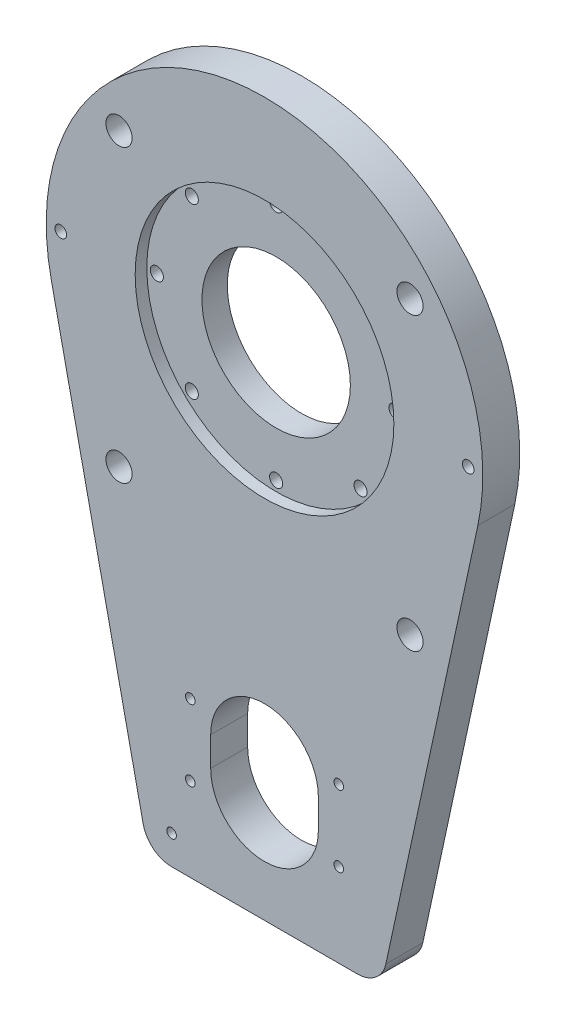
SolidWorks part; units mm, degrees
ref_plane "Front Plane" through (0, 0, 0) normal (0, 0, 1) x (1, 0, 0)
ref_plane "Top Plane" through (0, 0, 0) normal (0, 1, 0) x (1, 0, 0)
ref_plane "Right Plane" through (0, 0, 0) normal (1, 0, 0) x (0, 0, -1)
ref_plane "Plane1" through (0, 0, 12.7) normal (0, 0, 1) x (1, 0, 0)
sketch "Sketch1" plane through (0, 0, 12.7) normal (0, 0, 1) x (1, 0, 0)
  line L0 (40, -170) -> (73.3084, -15.8392)
  line L1 (-73.3084, -15.8392) -> (-40, -170)
  line L2 (-40, -170) -> (40, -170)
  arc A0 (73.3084, -15.8392) -> (-73.3084, -15.8392) centre (0, 0) ccw
extrude "Boss-Extrude1" add sketch "Sketch1" against normal blind 12.7
sketch "Sketch2" plane through (0, 0, 0) normal (0, 0, -1) x (-1, 0, 0)
  line L0 (-18.5, -124) -> (-18.5, -134)
  line L1 (18.5, -134) -> (18.5, -124)
  arc A0 (-18.5, -134) -> (18.5, -134) centre (0, -134) ccw
  arc A1 (18.5, -124) -> (-18.5, -124) centre (0, -124) ccw
extrude "Cut-Extrude1" cut sketch "Sketch2" against normal through all
hole_wizard "Hole1" positions "Sketch4" profile "Sketch3" legacy
sketch "Sketch4" plane through (0, 0, 0) normal (0, 0, -1) x (-1, 0, 0)
  point P0 (-50, -60)
  point P1 (50, -60)
  point P2 (50, 40)
  point P3 (-50, 40)
sketch "Sketch3" plane through (50, -60, 0) normal (1, 0, 0) x (0, 1, 0)
  line L0 (0, 0) -> (0, 12.7)
  line L1 (0, 12.7) -> (4.5, 12.7)
  line L2 (4.5, 12.7) -> (4.5, 0)
  line L3 (4.5, 0) -> (0, 0)
  line L4 (0, 110) -> (0, -10) construction
  dimension "Diameter" = 9
  dimension "Depth" = 12.7
hole_wizard "#4 Clearance Hole1" positions "Sketch6" profile "Sketch5" hole size "#4" standard "ANSI Inch"
sketch "Sketch6" plane through (0, 0, 12.7) normal (0, 0, 1) x (1, 0, 0)
  point P0 (-31.9299, -160)
  point P1 (-25.5, -116.75)
  point P2 (-25.5, -141.25)
  point P3 (25.5, -116.75)
  point P4 (25.5, -141.25)
sketch "Sketch5" plane through (-31.9299, -160, 12.7) normal (1, 0, 0) x (0, -1, 0)
  line L0 (0, 0) -> (0, 12.7)
  line L1 (0, 12.7) -> (1.65, 12.7)
  line L2 (1.65, 12.7) -> (1.65, 0)
  line L5 (1.65, 0) -> (0, 0)
  line L11 (0, -6.35) -> (0, 107.95) construction
  dimension "Thru Hole Dia." = 3.3
  dimension "Thru Hole Depth" = 12.7
hole_wizard "Hole2" positions "Sketch8" profile "Sketch7" legacy
sketch "Sketch8" plane through (0, 0, 12.7) normal (0, 0, 1) x (1, 0, 0)
  point P0 (0, 0)
sketch "Sketch7" plane through (0, 0, 12.7) normal (1, 0, 0) x (0, -1, 0)
  line L0 (0, 0) -> (0, 12.7)
  line L1 (0, 12.7) -> (25.5, 12.7)
  line L2 (25.5, 12.7) -> (25.5, 4)
  line L3 (25.5, 4) -> (44.45, 4)
  line L4 (44.45, 4) -> (44.45, 0)
  line L5 (44.45, 0) -> (0, 0)
  line L6 (0, 110) -> (0, -10) construction
  dimension "Diameter" = 51
  dimension "Depth" = 12.7
  dimension "C-Bore Diameter" = 88.9
  dimension "C-Bore Depth" = 4
hole_wizard "CBORE for #8 Binding Head Machine Screw1" positions "Sketch10" profile "Sketch9" counterbore size "#8" standard "ANSI Inch"
sketch "Sketch10" plane through (0, 0, 0) normal (0, 0, -1) x (-1, 0, 0)
  point P0 (28.9914, 28.9914)
  point P1 (41, 0)
  point P2 (28.9914, -28.9914)
  point P3 (0, -41)
  point P4 (-28.9914, -28.9914)
  point P5 (-41, 0)
  point P6 (-28.9914, 28.9914)
  point P7 (0, 41)
sketch "Sketch9" plane through (-28.9914, 28.9914, 0) normal (1, 0, 0) x (0, 1, 0)
  line L0 (0, 0) -> (0, 12.7)
  line L1 (0, 12.7) -> (2.25, 12.7)
  line L3 (2.25, 12.7) -> (2.25, 4)
  line L4 (2.25, 4) -> (4.125, 4)
  line L5 (4.125, 4) -> (4.125, 0)
  line L7 (4.125, 0) -> (0, 0)
  line L11 (0, -6.35) -> (0, 107.95) construction
  dimension "Thru Hole Dia." = 4.5
  dimension "Thru Hole Depth" = 12.7
  dimension "C'Bore Dia." = 8.25
  dimension "C'Bore Depth" = 4
fillet "Fillet1" radius 10 2 edges at (-40, -170, 6.35) (40, -170, 6.35)
sketch "Sketch11" plane through (0, 0, 12.7) normal (0, 0, 1) x (1, 0, 0)
  line L0 (-75, 0) -> (75, 0) construction
  arc A0 (73.3084, -15.8392) -> (-73.3084, -15.8392) centre (0, 0) ccw construction
  circle A1 centre (-70, 0) radius 2
  circle A2 centre (70, 0) radius 2
  dimension "D1" = 4
  dimension "D2" = 4
  dimension "D3" = 70
  dimension "D4" = 70
extrude "Cut-Extrude2" cut sketch "Sketch11" against normal through all
